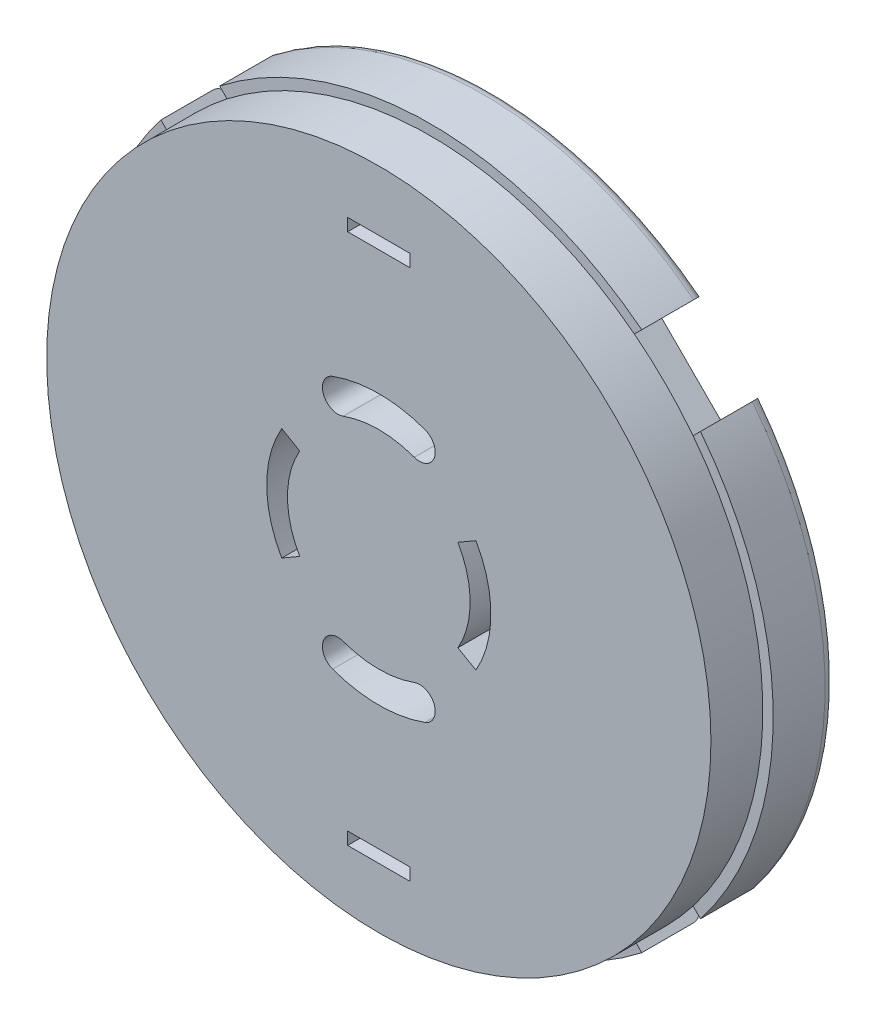
SolidWorks part; units mm, degrees
material "ABS"
ref_plane "Front Plane" through (0, 0, 0) normal (0, 0, 1) x (1, 0, 0)
ref_plane "Top Plane" through (0, 0, 0) normal (0, 1, 0) x (1, 0, 0)
ref_plane "Right Plane" through (0, 0, 0) normal (1, 0, 0) x (0, 0, -1)
sketch "Sketch1" plane through (0, 0, 0) normal (0, 0, 1) x (1, 0, 0)
  circle A0 centre (0, 0) radius 16.5
  dimension "D1" = 33
extrude "Boss-Extrude1" add sketch "Sketch1" against normal blind 3
sketch "Sketch2" plane through (0, 0, -3) normal (0, 0, -1) x (-1, 0, 0)
  circle A0 centre (0, 0) radius 3.75
  dimension "D1" = 7.5
extrude "Boss-Extrude2" add sketch "Sketch2" along normal blind 3
sketch "Sketch3" plane through (0, 0, -3) normal (0, 0, -1) x (-1, 0, 0)
  line L0 (10.253, 13.0815) -> (8.1317, 10.9602)
  line L5 (8.1317, 10.9602) -> (10.9602, 8.1317)
  line L6 (10.9602, 8.1317) -> (13.0815, 10.253)
  line L7 (13.0815, 10.253) -> (10.253, 13.0815)
  line L8 (0, 0) -> (9.5459, 9.5459) construction
  line L9 (0, 0) -> (0, 16.5) construction
  circle A0 centre (0, 0) radius 16.5 construction
  dimension "D2" = 4
  dimension "D1" = 45
  dimension "D3" = 3
extrude "Cut-Extrude1" cut sketch "Sketch3" against normal through all
pattern_circular "CirPattern1" count 4 over 360 about axis through (0, 0, 0) along (0, 0, 1) of "Cut-Extrude1"
sketch "Sketch4" plane through (0, 0, 0) normal (0, 0, 1) x (1, 0, 0)
  circle A0 centre (0, 0) radius 16
  dimension "D1" = 32
extrude "Boss-Extrude3" add sketch "Sketch4" along normal blind 2.5
sketch "Sketch6" plane through (0, 0, -3) normal (0, 0, -1) x (-1, 0, 0)
  line L0 (-4.6765, 2.7) -> (-3.8105, 2.2)
  line L1 (-4.6765, -2.7) -> (-3.8105, -2.2)
  line L2 (0, 0) -> (-4.4, 0) construction
  line L3 (-4.6765, 2.7) -> (-4.6765, -2.7) construction
  arc A0 (-4.6765, 2.7) -> (-4.6765, -2.7) centre (0, 0) ccw
  arc A1 (-3.8105, 2.2) -> (-3.8105, -2.2) centre (0, 0) ccw
  dimension "D1" = 1
  dimension "D2" = 4.4
  dimension "D3" = 60
  dimension "D4" = 5.4
extrude "Cut-Extrude2" cut sketch "Sketch6" against normal through all
pattern_circular "CirPattern2" count 2 over 360 about axis through (0, 0, 0) along (0, 0, 1) of "Cut-Extrude2"
sketch "Sketch7" plane through (0, 0, -3) normal (0, 0, -1) x (-1, 0, 0)
  line L0 (0, 0) -> (0, 5.75) construction
  line L1 (0, 0) -> (-1.9666, 5.4032) construction
  line L2 (0, 0) -> (1.9666, 5.4032) construction
  line L3 (-1.9666, 5.4032) -> (1.9666, 5.4032) construction
  arc A0 (-1.9666, 5.4032) -> (1.9666, 5.4032) centre (0, 0) cw construction
  arc A1 (2.2231, 6.108) -> (-2.2231, 6.108) centre (0, 0) ccw
  arc A2 (1.7101, 4.6985) -> (-1.7101, 4.6985) centre (0, 0) ccw
  arc A3 (1.7101, 4.6985) -> (2.2231, 6.108) centre (1.9666, 5.4032) ccw
  arc A4 (-2.2231, 6.108) -> (-1.7101, 4.6985) centre (-1.9666, 5.4032) ccw
  point P4 (0, 5.75)
  dimension "D1" = 0.75
  dimension "D2" = 5
  dimension "D3" = 40
  dimension "D4" = 3.9332
extrude "Cut-Extrude3" cut sketch "Sketch7" against normal through all
pattern_circular "CirPattern3" count 2 over 360 about axis through (0, 0, 0) along (0, 0, 1) of "Cut-Extrude3"
sketch "Sketch8" plane through (0, 0, -3) normal (0, 0, -1) x (-1, 0, 0)
  line L0 (8.4853, -3.5355) -> (3.5355, -8.4853)
  line L1 (3.5355, -8.4853) -> (5.6569, -10.6066)
  line L2 (5.6569, -10.6066) -> (10.6066, -5.6569)
  line L3 (10.6066, -5.6569) -> (8.4853, -3.5355)
  line L4 (0, 0) -> (6.0104, -6.0104) construction
  line L5 (0, 0) -> (0, -16.5) construction
  line L6 (0, 0) -> (-7.0711, 7.0711) construction
  arc A0 (-10.167, -12.9954) -> (10.167, -12.9954) centre (0, 0) ccw construction
  circle A1 centre (-7.0711, 7.0711) radius 1.45
  dimension "D5" = 2.9
  dimension "D1" = 45
  dimension "D2" = 7
  dimension "D3" = 3
  dimension "D4" = 8.5
  dimension "D6" = 10
extrude "Cut-Extrude4" cut sketch "Sketch8" against normal blind 0.5
sketch "Sketch9" plane through (0, 0, -2.5) normal (0, 0, -1) x (-1, 0, 0)
  line L0 (-7.0711, 5.6211) -> (-7.0711, 8.5211)
  circle A0 centre (-7.0711, 7.0711) radius 1.45 construction
  circle A1 centre (-7.0711, 7.0711) radius 1.45 construction
extrude "Extrude-Thin1" add sketch "Sketch9" along normal up to surface (0.5 mm away) thin up to face at (-7.0711, -7.0711, -3) thin type two direction wall 0.25 second wall 0.25
sketch "Sketch10" plane through (0, 0, -2.5) normal (0, 0, -1) x (-1, 0, 0)
  line L0 (-8.5211, 7.0711) -> (-5.6211, 7.0711)
  arc A0 (-7.3211, 8.4994) -> (-7.3211, 5.6428) centre (-7.0711, 7.0711) ccw construction
  arc A1 (-6.8211, 5.6428) -> (-6.8211, 8.4994) centre (-7.0711, 7.0711) ccw construction
extrude "Extrude-Thin2" add sketch "Sketch10" along normal up to surface (0.5 mm away) thin up to face at (6.2211, 7.0711, -3) thin type two direction wall 0.25 second wall 0.25
sketch "Sketch11" plane through (0, 0, -3) normal (0, 0, -1) x (-1, 0, 0)
  line L0 (0, 0) -> (0, 12.8) construction
  line L1 (-1.5, 13.1) -> (1.5, 13.1)
  line L2 (-1.5, 13.1) -> (-1.5, 12.5)
  line L3 (-1.5, 12.5) -> (1.5, 12.5)
  line L4 (1.5, 13.1) -> (1.5, 12.5)
  line L5 (-1.5, 13.1) -> (1.5, 12.5) construction
  line L6 (-1.5, 12.5) -> (1.5, 13.1) construction
  point P0 (0, 12.8)
  dimension "D1" = 3
  dimension "D2" = 0.6
  dimension "D3" = 12.5
extrude "Cut-Extrude5" cut sketch "Sketch11" against normal through all
pattern_circular "CirPattern4" count 2 over 360 about axis through (0, 0, 0) along (0, 0, 1) of "Cut-Extrude5"
fillet "Fillet1" radius 0.1 2 edges at (-3.75, 0, -6) (-3.75, 0, -3)
fillet "Fillet2" radius 0.5 4 edges at (16.5, 0, -3) (0, -16.5, -3) (-16.5, 0, -3) (0, 16.5, -3)
